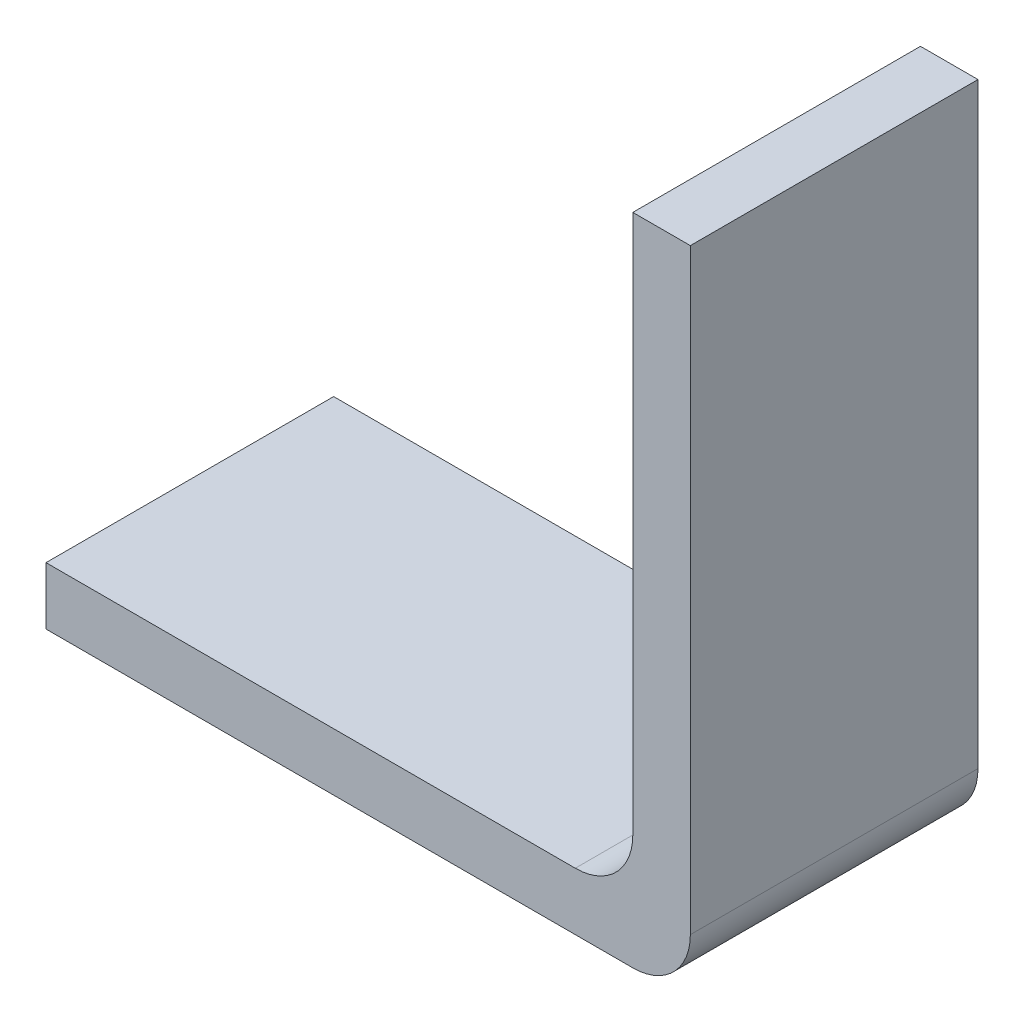
SolidWorks part; units mm, degrees
ref_plane "Ön Düzlem" through (0, 0, 0) normal (0, 0, 1) x (1, 0, 0)
ref_plane "Üst Düzlem" through (0, 0, 0) normal (0, 1, 0) x (1, 0, 0)
ref_plane "Sağ Düzlem" through (0, 0, 0) normal (1, 0, 0) x (0, 0, -1)
sketch "Çizim1" plane through (0, 0, 0) normal (0, 0, 1) x (1, 0, 0)
  line L0 (82.9905, -22.3088) -> (82.9905, -33.6814)
  line L2 (82.9905, -33.6814) -> (71.7905, -33.6814)
  dimension "D1" = 11.2
extrude "Ekstrüzyon-İnce2" add sketch "Çizim1" along normal blind 5 thin
fillet "Radyus1" radius 1 2 edges at (81.9905, -32.6814, 2.5) (82.9905, -33.6814, 2.5)
